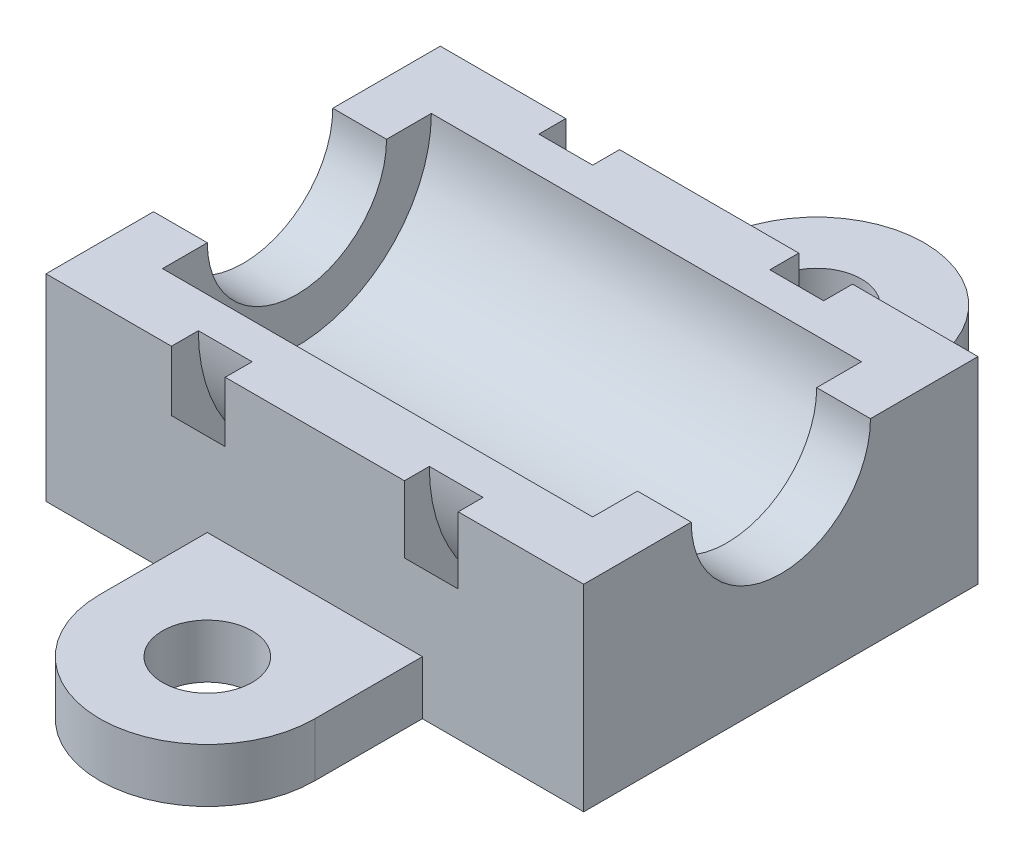
SolidWorks part; units mm, degrees
ref_plane "Alzado" through (0, 0, 0) normal (0, 0, 1) x (1, 0, 0)
ref_plane "Planta" through (0, 0, 0) normal (0, 1, 0) x (1, 0, 0)
ref_plane "Vista lateral" through (0, 0, 0) normal (1, 0, 0) x (0, 0, -1)
sketch "Croquis1" plane through (0, 0, 0) normal (0, 1, 0) x (1, 0, 0)
  line L0 (0, 0) -> (30, 0)
  line L1 (30, 0) -> (30, 22)
  line L2 (30, 22) -> (0, 22)
  line L3 (0, 22) -> (0, 0)
  dimension "D1" = 30
  dimension "D2" = 22
extrude "Saliente-Extruir1" add sketch "Croquis1" along normal blind 11
sketch "Croquis2" plane through (0, 0, 0) normal (0, -1, 0) x (1, 0, 0)
  line L0 (0, -11) -> (30, -11) construction
  line L1 (0, 0) -> (30, 0) construction
  line L2 (0, -22) -> (0, 0) construction
  line L3 (21, 6) -> (21, 0)
  line L4 (21, 0) -> (9, 0)
  line L5 (9, 0) -> (9, 6)
  line L6 (30, 0) -> (30, -22) construction
  line L7 (9, -22) -> (9, -28)
  line L8 (21, -22) -> (9, -22)
  line L9 (21, -28) -> (21, -22)
  arc A0 (21, 6) -> (9, 6) centre (15, 6) ccw
  circle A1 centre (15, 6) radius 2.5
  circle A2 centre (15, -28) radius 2.5
  arc A3 (21, -28) -> (9, -28) centre (15, -28) cw
  dimension "D2" = 5
  dimension "D1" = 6
  dimension "D3" = 6
extrude "Saliente-Extruir2" add sketch "Croquis2" against normal blind 3
sketch "Croquis3" plane through (0, 0, 0) normal (-1, 0, 0) x (0, 0, 1)
  line L0 (-22, 11) -> (0, 11) construction
  circle A0 centre (-11, 11) radius 5
  dimension "D1" = 10
extrude "Cortar-Extruir1" cut sketch "Croquis3" against normal through all
ref_plane "Plano1" through (10, 0, 0) normal (-1, 0, 0) x (0, 0, 1)
sketch "Croquis4" plane through (10, 0, 0) normal (-1, 0, 0) x (0, 0, 1)
  circle A3 centre (-11, 11) radius 11.5
  circle A4 centre (-11, 11) radius 9.5
  dimension "D1" = 23
  dimension "D2" = 2
ref_plane "Plano2" through (3, 0, 0) normal (-1, 0, 0) x (0, 0, 1)
extrude "Cortar-Extruir13" cut sketch "Croquis4" along normal blind 3
ref_plane "Plano3" through (20, 0, 0) normal (1, 0, 0) x (0, 0, -1)
sketch "Croquis6" plane through (20, 0, 0) normal (1, 0, 0) x (0, 0, -1)
  circle A2 centre (10.8872, 10.9727) radius 11.5
  circle A3 centre (10.8872, 10.9727) radius 9.5
  point P8 (0, 0)
  dimension "D1" = 23
extrude "Cortar-Extruir14" cut sketch "Croquis6" along normal blind 3
sketch "Croquis7" plane through (3, 0, 0) normal (-1, 0, 0) x (0, 0, 1)
  circle A0 centre (-11, 11) radius 7.5
  dimension "D1" = 15
extrude "Cortar-Extruir15" cut sketch "Croquis7" against normal offset from surface (24 mm away) 3 up to face at (30, 6.5, -11)
